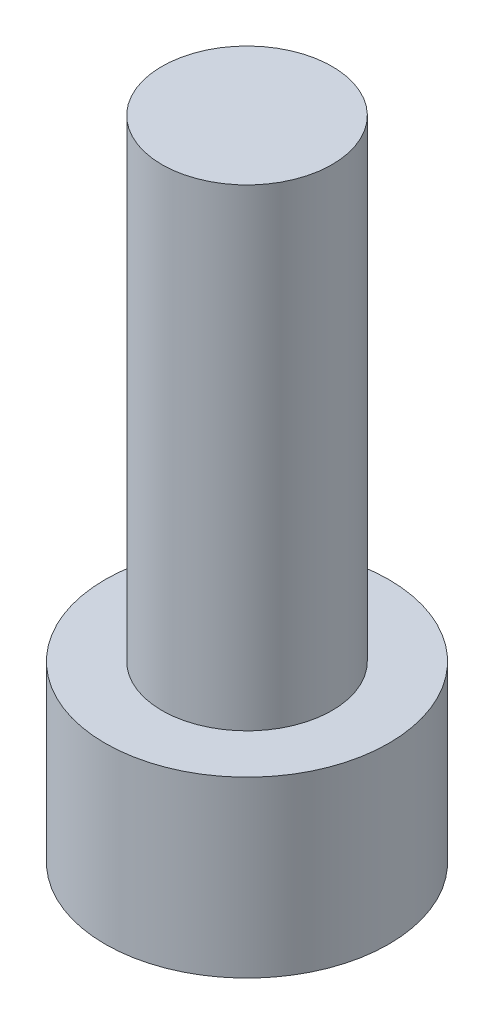
SolidWorks part; units mm, degrees
ref_plane "Front Plane" through (0, 0, 0) normal (0, 0, 1) x (1, 0, 0)
ref_plane "Top Plane" through (0, 0, 0) normal (0, 1, 0) x (1, 0, 0)
ref_plane "Right Plane" through (0, 0, 0) normal (1, 0, 0) x (0, 0, -1)
sketch "Sketch1" plane through (0, 0, 0) normal (0, 1, 0) x (1, 0, 0)
  circle A0 centre (0, 0) radius 2.8575
  dimension "D1" = 5.715
extrude "Boss-Extrude1" add sketch "Sketch1" along normal blind 3.5052
sketch "Sketch2" plane through (0, 0, 0) normal (0, -1, 0) x (1, 0, 0)
  line L1 (1.604, 0) -> (0.802, 1.3891)
  line L2 (0.802, 1.3891) -> (-0.802, 1.3891)
  line L3 (-0.802, 1.3891) -> (-1.604, 0)
  line L4 (-1.604, 0) -> (-0.802, -1.3891)
  line L5 (-0.802, -1.3891) -> (0.802, -1.3891)
  line L6 (0.802, -1.3891) -> (1.604, 0)
  circle A0 centre (0, 0) radius 1.3891 construction
  dimension "D1" = 2.7781
extrude "Cut-Extrude1" cut sketch "Sketch2" against normal blind 1.9558
sketch "Sketch3" plane through (0, 3.5052, 0) normal (0, 1, 0) x (1, 0, 0)
  circle A0 centre (0, 0) radius 1.7145
  dimension "D1" = 3.429
extrude "Boss-Extrude2" add sketch "Sketch3" along normal blind 9.525
